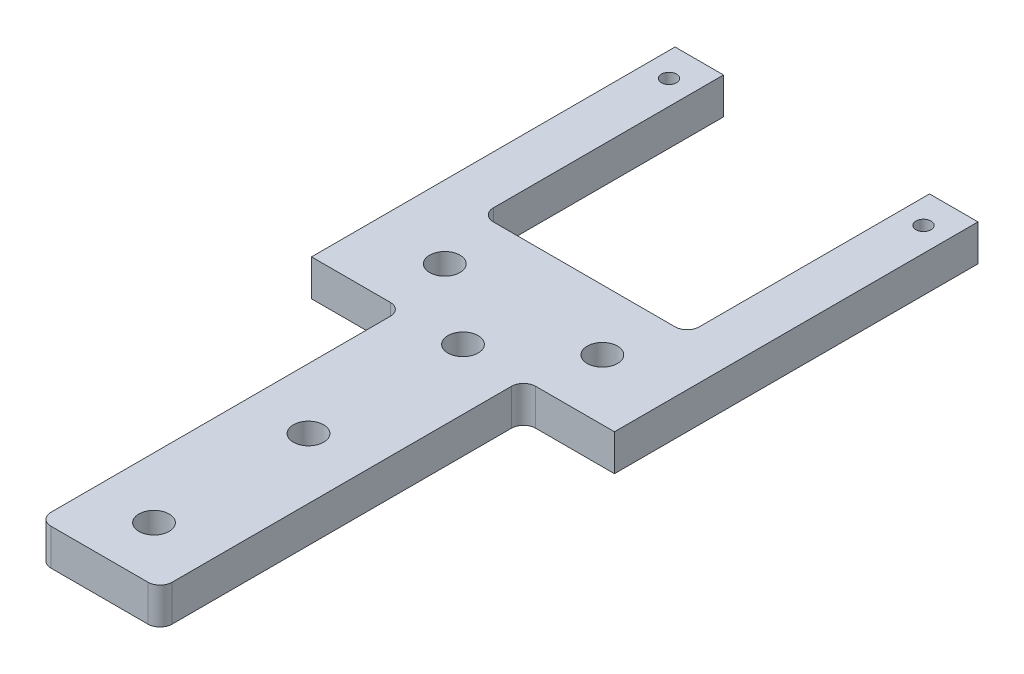
SolidWorks part; units mm, degrees
ref_plane "Front Plane" through (0, 0, 0) normal (0, 0, 1) x (1, 0, 0)
ref_plane "Top Plane" through (0, 0, 0) normal (0, 1, 0) x (1, 0, 0)
ref_plane "Right Plane" through (0, 0, 0) normal (1, 0, 0) x (0, 0, -1)
sketch "Sketch1" plane through (0, 0, 0) normal (0, 1, 0) x (1, 0, 0)
  line L0 (0, -1000) -> (0, 49000) construction
  line L1 (-5, -30) -> (5, -30)
  line L2 (-5, -30) -> (-5, 0)
  line L3 (-5, 0) -> (5, 0)
  line L4 (5, -30) -> (5, 0)
  line L5 (-12.5, 0) -> (12.5, 0)
  line L6 (-12.5, 0) -> (-12.5, 10)
  line L7 (-12.5, 10) -> (12.5, 10)
  line L8 (12.5, 0) -> (12.5, 10)
  line L9 (-8.5, 10) -> (-12.5, 10)
  line L10 (-8.5, 10) -> (-8.5, 30)
  line L11 (-8.5, 30) -> (-12.5, 30)
  line L12 (-12.5, 10) -> (-12.5, 30)
  line L13 (8.5, 10) -> (12.5, 10)
  line L14 (8.5, 10) -> (8.5, 30)
  line L15 (8.5, 30) -> (12.5, 30)
  line L16 (12.5, 10) -> (12.5, 30)
  circle A0 centre (-10.5, 27.5) radius 0.625
  circle A1 centre (-6.5, 5) radius 1.25
  circle A2 centre (0, 0) radius 1.25
  circle A3 centre (0, -12.75) radius 1.25
  circle A4 centre (0, -25.5) radius 1.25
  circle A5 centre (10.5, 27.5) radius 0.625
  circle A6 centre (6.5, 5) radius 1.25
  point P14 (0, 0)
  point P16 (0, 0)
  point P33 (0, 0)
  point P34 (-12.5, 5)
  point P35 (0, 0)
  point P36 (0, 0)
  point P37 (-10.5, 30)
  dimension "D7" = 1.25
  dimension "D8" = 2.5
  dimension "D9" = 6
  dimension "D11" = 12.75
  dimension "D12" = 2.5
  dimension "D1" = 4
  dimension "D2" = 30
  dimension "D3" = 25
  dimension "D4" = 10
  dimension "D5" = 30
  dimension "D6" = 10
  dimension "D10" = 12.75
extrude "Boss-Extrude1" add sketch "Sketch1" along normal mid plane 3 contours L0 L1 L4 L3 A2 A3 A4 | L1 L0 A4 A3 A2 L3 L2 | A2 L0 L7 L6 L5 L3 A1 | L0 A2 L3 L5 L8 L7 A6 | L7 L16 L15 L14 A5 | L12 L7 L10 L11 A0
fillet "Fillet1" radius 1 6 edges at (5, 0, 30) (-5, 0, 30) (-5, 0, 0) (5, 0, 0) (8.5, 0, -10) (-8.5, 0, -10)
